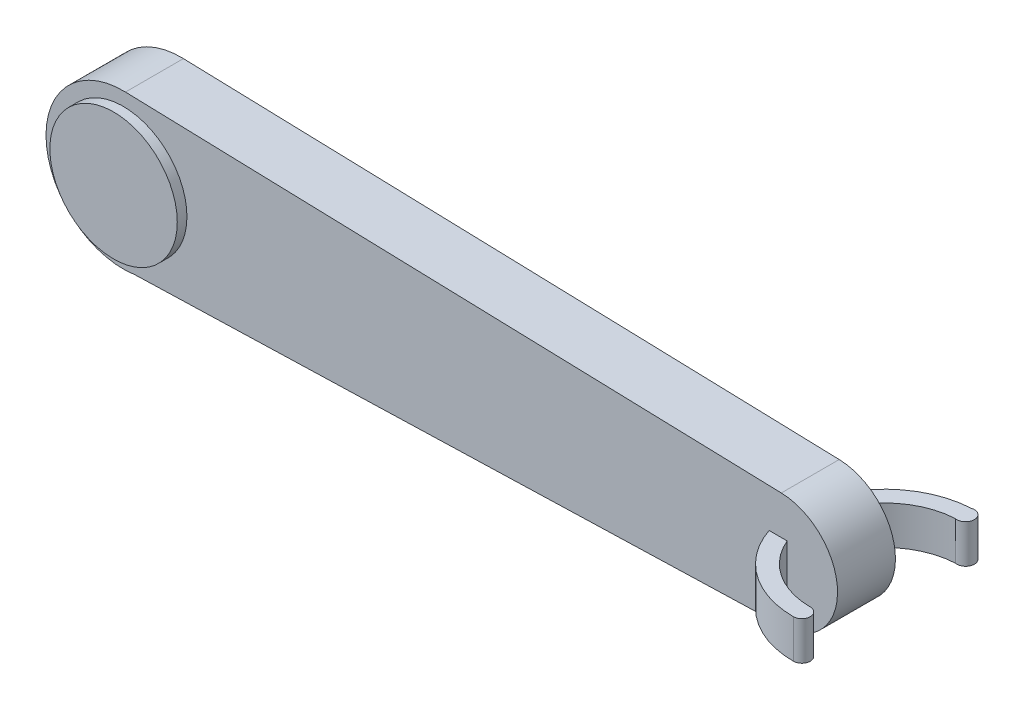
SolidWorks part; units mm, degrees
ref_plane "Front Plane" through (0, 0, 0) normal (0, 0, 1) x (1, 0, 0)
ref_plane "Top Plane" through (0, 0, 0) normal (0, 1, 0) x (1, 0, 0)
ref_plane "Right Plane" through (0, 0, 0) normal (1, 0, 0) x (0, 0, -1)
sketch "Sketch1" plane through (0, 0, 0) normal (0, 0, 1) x (1, 0, 0)
  line L0 (0, 0) -> (-85, 0)
  line L1 (0, 0) -> (85, 0)
  line L2 (-84.4118, 19.9913) -> (85.4412, 14.9935)
  line L3 (-81.9839, -19.7713) -> (88.3501, -14.6211)
  circle A0 centre (-85, 0) radius 20
  circle A1 centre (85, 0) radius 15
  dimension "D3" = 40
  dimension "D4" = 30
  dimension "D1" = 85
  dimension "D2" = 85
extrude "Boss-Extrude1" add sketch "Sketch1" along normal mid plane 15
sketch "Sketch3" plane through (0, 0, 7.5) normal (0, 0, 1) x (1, 0, 0)
  circle A0 centre (-85, 0) radius 16.5
  dimension "D1" = 33
extrude "Boss-Extrude2" add sketch "Sketch3" along normal mid plane 5 contours A0
sketch "Sketch6" plane through (0, 0, 7.5) normal (0, 0, 1) x (1, 0, 0)
  circle A0 centre (85, 0) radius 5
  dimension "D1" = 10
sketch "Sketch7" plane through (0, 0, -7.5) normal (0, 0, -1) x (-1, 0, 0)
  circle A0 centre (85, 0) radius 5
  dimension "D1" = 10
extrude "Boss-Extrude3" add sketch "Sketch7" along normal blind 10
sketch "Sketch12" plane through (0, 0, 0) normal (0, 1, 0) x (1, 0, 0)
  line L1 (81.0687, 0) -> (85.4412, 0)
  arc A0 (104.7608, -19.3196) -> (104.7608, 19.3196) centre (104.7608, 0) cw
  arc A1 (104.7608, 23.6921) -> (104.7608, -23.6921) centre (104.7608, 0) ccw
  circle A2 centre (104.7608, -21.5059) radius 2.1863
  circle A3 centre (104.1771, 21.5059) radius 2.2628
  dimension "D1" = 19.3196
extrude "Boss-Extrude4" add sketch "Sketch12" along normal mid plane 10 contours A3 A1 L1 A0 | A2 A0 L1 A1
